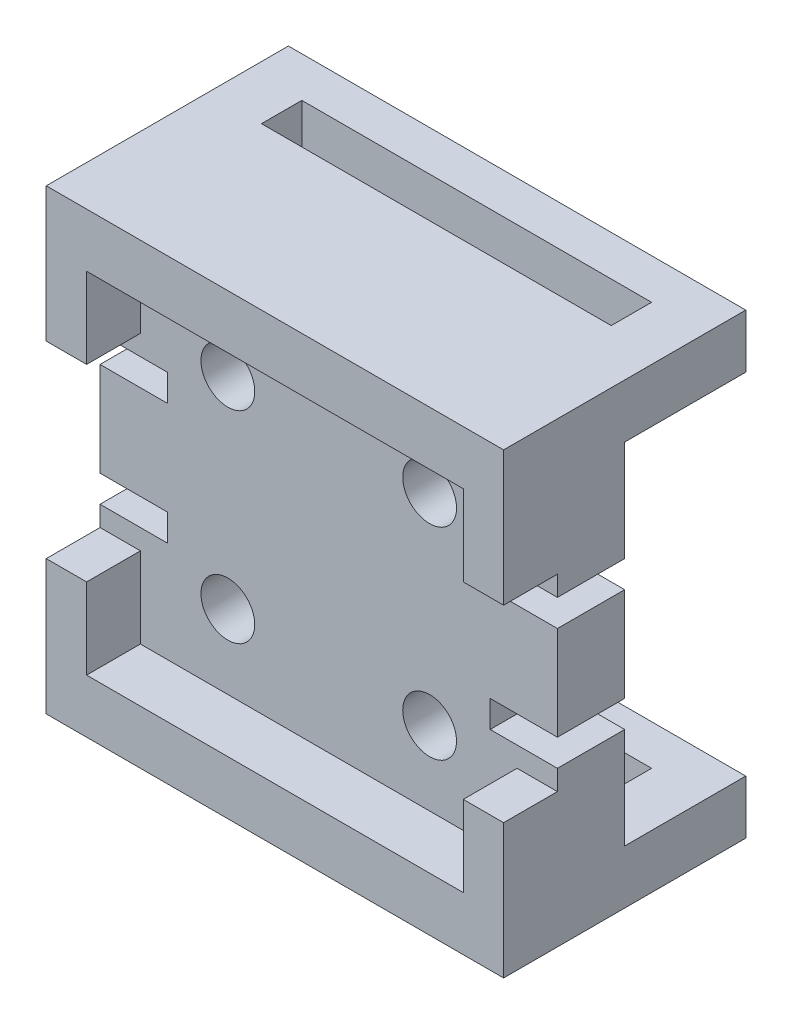
SolidWorks part; units mm, degrees
ref_plane "Piano frontale" through (0, 0, 0) normal (0, 0, 1) x (1, 0, 0)
ref_plane "Piano superiore" through (0, 0, 0) normal (0, 1, 0) x (1, 0, 0)
ref_plane "Piano destro" through (0, 0, 0) normal (1, 0, 0) x (0, 0, -1)
sketch "Sketch1" plane through (0, 0, 0) normal (0, 0, 1) x (1, 0, 0)
  line L0 (0, 34) -> (34, 0) construction
  line L1 (0, 0) -> (34, 0)
  line L2 (0, 0) -> (0, 34)
  line L3 (0, 34) -> (34, 34)
  line L4 (34, 0) -> (34, 34)
  line L5 (9.5, 24.5) -> (24.5, 24.5) construction
  line L6 (9.5, 24.5) -> (9.5, 9.5) construction
  line L7 (9.5, 9.5) -> (24.5, 9.5) construction
  line L8 (24.5, 24.5) -> (24.5, 9.5) construction
  line L9 (9.5, 9.5) -> (24.5, 24.5) construction
  line L10 (17, 17) -> (24.5, 17) construction
  circle A0 centre (24.5, 24.5) radius 2
  circle A1 centre (9.5, 24.5) radius 2
  circle A2 centre (9.5, 9.5) radius 2
  circle A3 centre (24.5, 9.5) radius 2
  point P9 (17, 17)
  point P10 (17, 17)
  dimension "D5" = 4
  dimension "D1" = 34
  dimension "D2" = 34
  dimension "D3" = 15
  dimension "D4" = 15
extrude "Body" add sketch "Sketch1" along normal blind 5
sketch "Sketch2" plane through (0, 0, 0) normal (0, 0, -1) x (-1, 0, 0)
  line L0 (0, 34) -> (0, 0) construction
  line L1 (-34, 34) -> (0, 34)
  line L2 (-34, 34) -> (-34, 30)
  line L3 (-34, 30) -> (0, 30)
  line L4 (0, 34) -> (0, 30)
  line L6 (-34, 0) -> (0, 0)
  line L7 (-34, 0) -> (-34, 4)
  line L8 (-34, 4) -> (0, 4)
  line L9 (0, 0) -> (0, 4)
  dimension "D1" = 4
  dimension "D2" = 4
extrude "Leg1" add sketch "Sketch2" along normal blind 3
sketch "Sketch3" plane through (0, 0, -3) normal (0, 0, -1) x (-1, 0, 0)
  line L0 (-34, 30) -> (0, 30) construction
  line L1 (-34, 34) -> (-30, 34)
  line L2 (-34, 34) -> (-34, 30)
  line L3 (-34, 30) -> (-30, 30)
  line L4 (-30, 34) -> (-30, 30)
  line L5 (-17, 34) -> (-17, 0) construction
  line L6 (0, 34) -> (-34, 34) construction
  line L7 (-34, 0) -> (0, 0) construction
  line L8 (-17, 17) -> (0, 17) construction
  line L9 (0, 30) -> (0, 4) construction
  line L10 (-17, 17) -> (-34, 17) construction
  line L11 (-34, 4) -> (-34, 30) construction
  line L12 (0, 30) -> (-4, 30)
  line L13 (-4, 34) -> (-4, 30)
  line L14 (0, 34) -> (-4, 34)
  line L15 (0, 34) -> (0, 30)
  line L16 (0, 0) -> (0, 4)
  line L17 (0, 0) -> (-4, 0)
  line L18 (-4, 0) -> (-4, 4)
  line L19 (0, 4) -> (-4, 4)
  line L20 (-34, 4) -> (-30, 4)
  line L21 (-30, 0) -> (-30, 4)
  line L22 (-34, 0) -> (-30, 0)
  line L23 (-34, 0) -> (-34, 4)
  dimension "D1" = 4
  dimension "D2" = 26
extrude "Leg2" add sketch "Sketch3" along normal blind 3
sketch "Sketch4" plane through (0, 0, -6) normal (0, 0, -1) x (-1, 0, 0)
  line L1 (-34, 34) -> (0, 34)
  line L2 (-34, 34) -> (-34, 30)
  line L3 (-34, 30) -> (0, 30)
  line L4 (0, 34) -> (0, 30)
  line L5 (-34, 4) -> (0, 4)
  line L6 (-34, 4) -> (-34, 0)
  line L7 (-34, 0) -> (0, 0)
  line L8 (0, 4) -> (0, 0)
extrude "Leg3" add sketch "Sketch4" along normal blind 3
sketch "Sketch5" plane through (0, 0, 5) normal (0, 0, 1) x (1, 0, 0)
  line L0 (34, 0) -> (34, 34) construction
  line L1 (0, 34) -> (34, 34)
  line L2 (0, 34) -> (0, 30)
  line L3 (3, 30) -> (31, 30)
  line L4 (34, 34) -> (34, 30)
  line L5 (3, 24) -> (0, 24)
  line L11 (0, 30) -> (0, 24)
  line L13 (3, 30) -> (3, 24)
  line L18 (34, 34) -> (0, 34) construction
  line L19 (31, 30) -> (31, 24)
  line L20 (31, 24) -> (34, 24)
  line L21 (34, 24) -> (34, 30)
  line L22 (0, 34) -> (0, 0) construction
  line L23 (0, 17) -> (34, 17) construction
  line L24 (31, 10) -> (34, 10)
  line L25 (31, 4) -> (31, 10)
  line L26 (3, 4) -> (31, 4)
  line L27 (3, 4) -> (3, 10)
  line L28 (3, 10) -> (0, 10)
  line L29 (0, 4) -> (0, 10)
  line L30 (0, 0) -> (0, 4)
  line L31 (0, 0) -> (34, 0)
  line L32 (34, 0) -> (34, 4)
  line L33 (34, 10) -> (34, 4)
  dimension "D1" = 4
  dimension "D3" = 3
  dimension "D4" = 6
  dimension "D5" = 14
extrude "Walls" add sketch "Sketch5" along normal blind 4
sketch "Sketch6" plane through (0, 0, 5) normal (0, 0, 1) x (1, 0, 0)
  line L0 (0, 24) -> (0, 10) construction
  line L1 (0, 22.5) -> (5, 22.5)
  line L2 (0, 22.5) -> (0, 20.5)
  line L3 (0, 20.5) -> (5, 20.5)
  line L4 (5, 22.5) -> (5, 20.5)
  line L5 (0, 17) -> (34, 17) construction
  line L6 (34, 10) -> (34, 24) construction
  line L7 (17, 34) -> (17, 0) construction
  line L8 (34, 34) -> (0, 34) construction
  line L9 (0, 0) -> (34, 0) construction
  line L10 (34, 20.5) -> (29, 20.5)
  line L11 (29, 22.5) -> (29, 20.5)
  line L12 (34, 22.5) -> (29, 22.5)
  line L13 (34, 22.5) -> (34, 20.5)
  line L14 (0, 13.5) -> (5, 13.5)
  line L15 (5, 11.5) -> (5, 13.5)
  line L16 (0, 11.5) -> (5, 11.5)
  line L17 (0, 11.5) -> (0, 13.5)
  line L18 (34, 11.5) -> (34, 13.5)
  line L19 (34, 11.5) -> (29, 11.5)
  line L20 (29, 11.5) -> (29, 13.5)
  line L21 (34, 13.5) -> (29, 13.5)
  dimension "D1" = 5
  dimension "D2" = 2
  dimension "D3" = 3.5
extrude "Cut-Extrude1" cut sketch "Sketch6" against normal blind 5
